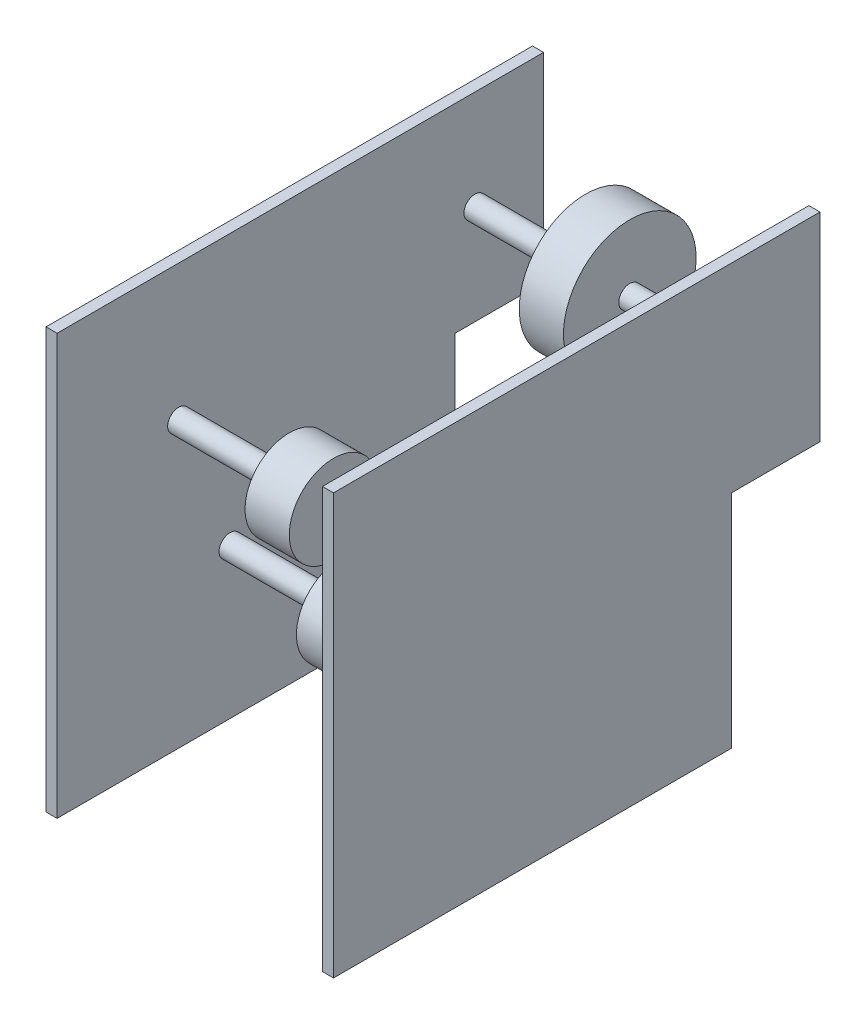
SolidWorks part; units mm, degrees
ref_plane "Front Plane" through (0, 0, 0) normal (0, 0, 1) x (1, 0, 0)
ref_plane "Top Plane" through (0, 0, 0) normal (0, 1, 0) x (1, 0, 0)
ref_plane "Right Plane" through (0, 0, 0) normal (1, 0, 0) x (0, 0, -1)
sketch "Sketch1" plane through (0, 0, 0) normal (1, 0, 0) x (0, 0, -1)
  line L1 (0, 0) -> (228.6, 0)
  line L2 (0, 0) -> (0, 241.3)
  line L3 (0, 241.3) -> (279.4, 241.3)
  line L5 (228.6, 127) -> (228.6, 0)
  line L8 (228.6, 127) -> (279.4, 127)
  line L9 (279.4, 241.3) -> (279.4, 127)
  line L11 (0, 369.5588) -> (317.5, 369.5588) construction
  line L12 (0, 369.5588) -> (0, 344.1588) construction
  line L13 (0, 344.1588) -> (317.5, 344.1588) construction
  line L14 (317.5, 369.5588) -> (317.5, 344.1588) construction
  line L15 (82.55, 369.5588) -> (234.95, 369.5588) construction
  line L16 (82.55, 369.5588) -> (82.55, 407.6588) construction
  line L17 (82.55, 407.6588) -> (234.95, 407.6588) construction
  line L18 (234.95, 369.5588) -> (234.95, 407.6588) construction
  circle A0 centre (384.0059, 76.5108) radius 76.2 construction
  circle A1 centre (240.0173, 184.15) radius 38.1 construction
  circle A2 centre (161.4722, 31.75) radius 25.4 construction
  circle A3 centre (99.3568, 86.1208) radius 25.4 construction
  circle A4 centre (69.85, 163.2172) radius 25.4 construction
  arc A5 (240.0173, 12.7) -> (69.85, 163.2172) centre (240.0173, 184.15) cw construction
  point P26 (158.75, 407.6588)
  point P27 (158.75, 344.1588)
  dimension "D1" = 152.4
  dimension "D2" = 50.8
  dimension "D3" = 76.2
  dimension "D4" = 133.35
  dimension "D5" = 146.05
  dimension "D6" = 31.75
  dimension "D7" = 82.55
  dimension "D8" = 82.55
  dimension "D9" = 69.85
  dimension "D10" = 57.15
  dimension "D11" = 127
  dimension "D12" = 279.4
  dimension "D13" = 228.6
  dimension "D14" = 114.3
  dimension "D15" = 25.4
  dimension "D16" = 317.5
  dimension "D17" = 38.1
  dimension "D18" = 152.4
extrude "Boss-Extrude1" add sketch "Sketch1" along normal mid plane 165.1
sketch "Sketch2" plane through (0, 241.3, 0) normal (0, 1, 0) x (1, 0, 0)
  line L0 (82.55, 0) -> (-82.55, 0) construction
  line L1 (-76.2, 0) -> (76.2, 0)
  line L2 (-76.2, 0) -> (-76.2, 279.4)
  line L4 (76.2, 0) -> (76.2, 279.4)
  line L6 (-82.55, 279.4) -> (-82.55, 0) construction
  line L7 (82.55, 279.4) -> (82.55, 0) construction
  line L8 (82.55, 279.4) -> (-82.55, 279.4) construction
  line L9 (-76.2, 279.4) -> (76.2, 279.4)
  dimension "D1" = 6.35
  dimension "D2" = 6.35
extrude "Cut-Extrude1" cut sketch "Sketch2" against normal through all
sketch "Sketch3" plane through (0, 0, 0) normal (1, 0, 0) x (0, 0, -1)
  circle A0 centre (161.4722, 31.75) radius 25.4 construction
  circle A1 centre (240.0173, 184.15) radius 38.1 construction
  circle A2 centre (69.85, 163.2172) radius 25.4 construction
  circle A3 centre (99.3568, 86.1208) radius 25.4 construction
  circle A4 centre (161.4722, 31.75) radius 25.4
  circle A5 centre (240.0173, 184.15) radius 38.1
  circle A6 centre (69.85, 163.2172) radius 25.4
  circle A7 centre (99.3568, 86.1208) radius 25.4
extrude "Boss-Extrude2" add sketch "Sketch3" along normal mid plane 25.4 separate body
sketch "Sketch4" plane through (0, 0, 0) normal (1, 0, 0) x (0, 0, -1)
  circle A0 centre (69.85, 163.2172) radius 6.35
  circle A1 centre (99.3568, 86.1208) radius 6.35
  circle A2 centre (161.4722, 31.75) radius 6.35
  circle A3 centre (240.0173, 184.15) radius 6.35
  dimension "D1" = 12.7
extrude "Boss-Extrude3" add sketch "Sketch4" along normal mid plane 152.4
